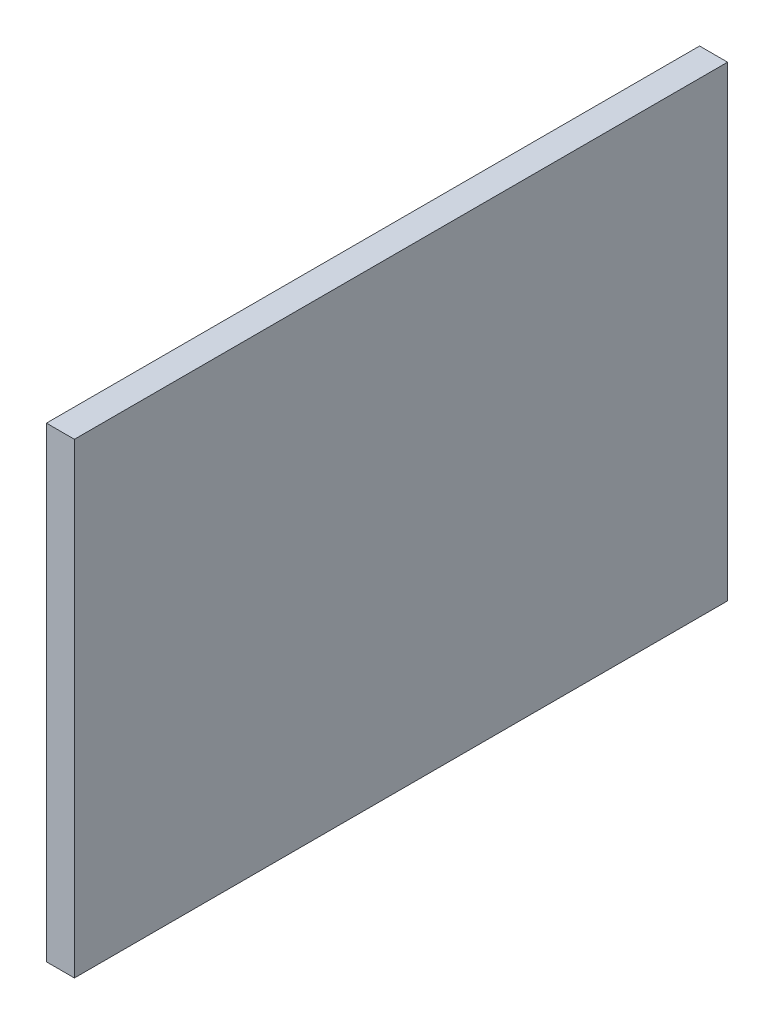
SolidWorks part; units mm, degrees
ref_plane "Front Plane" through (0, 0, 0) normal (0, 0, 1) x (1, 0, 0)
ref_plane "Top Plane" through (0, 0, 0) normal (0, 1, 0) x (1, 0, 0)
ref_plane "Right Plane" through (0, 0, 0) normal (1, 0, 0) x (0, 0, -1)
sketch "Sketch1" plane through (0, 0, 0) normal (1, 0, 0) x (0, 0, -1)
  line L1 (-51.1787, 32.9884) -> (18.8213, 32.9884)
  line L2 (-51.1787, 32.9884) -> (-51.1787, -17.0116)
  line L3 (-51.1787, -17.0116) -> (18.8213, -17.0116)
  line L4 (18.8213, 32.9884) -> (18.8213, -17.0116)
  dimension "D1" = 50
  dimension "D2" = 70
extrude "Boss-Extrude1" add sketch "Sketch1" along normal blind 3
